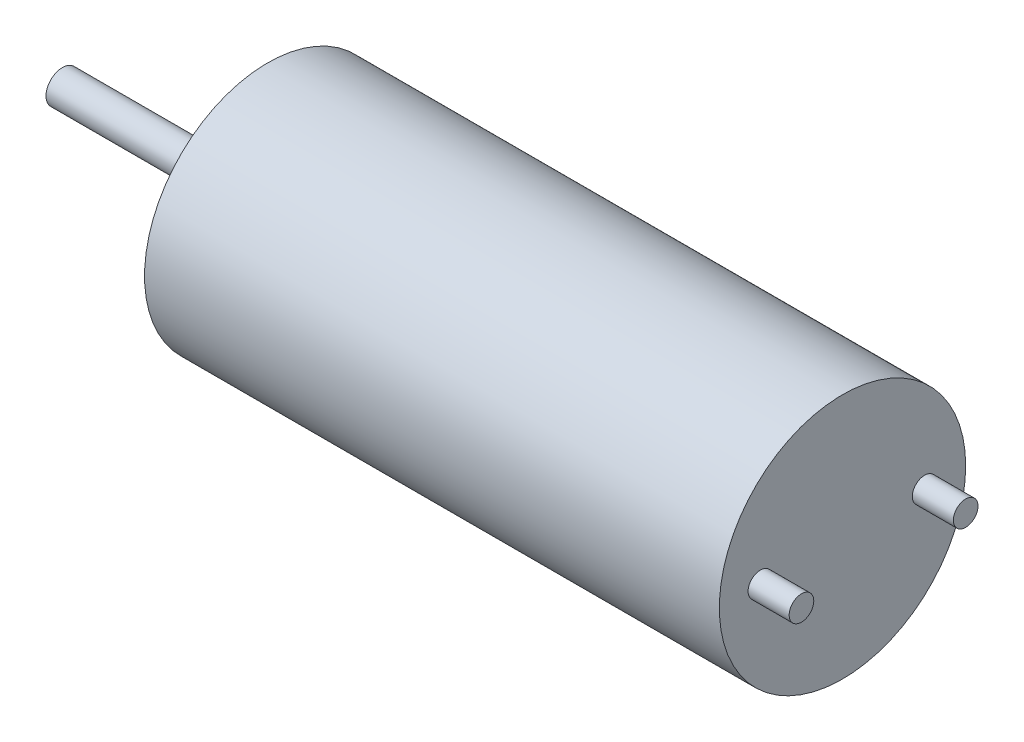
SolidWorks part; units mm, degrees
ref_plane "Front Plane" through (0, 0, 0) normal (0, 0, 1) x (1, 0, 0)
ref_plane "Top Plane" through (0, 0, 0) normal (0, 1, 0) x (1, 0, 0)
ref_plane "Right Plane" through (0, 0, 0) normal (1, 0, 0) x (0, 0, -1)
sketch "Sketch1" plane through (0, 0, 0) normal (1, 0, 0) x (0, 0, -1)
  circle A0 centre (0, 0) radius 3
  dimension "D1" = 6
extrude "Boss-Extrude1" add sketch "Sketch1" along normal blind 14
sketch "Sketch2" plane through (0, 0, 0) normal (-1, 0, 0) x (0, 0, 1)
  circle A0 centre (0, 0) radius 1.2
  dimension "D1" = 2.4
extrude "Boss-Extrude2" add sketch "Sketch2" along normal blind 0.8
sketch "Sketch3" plane through (-0.8, 0, 0) normal (-1, 0, 0) x (0, 0, 1)
  circle A0 centre (0, 0) radius 0.4
  dimension "D1" = 0.8
extrude "Boss-Extrude3" add sketch "Sketch3" along normal blind 4.2
sketch "Sketch4" plane through (14, 0, 0) normal (1, 0, 0) x (0, 0, -1)
  line L0 (-2, 0) -> (2, 0) construction
  circle A0 centre (-2, 0) radius 0.3
  circle A1 centre (2, 0) radius 0.3
  point P4 (0, 0)
  dimension "D2" = 0.6
  dimension "D1" = 4
extrude "Boss-Extrude4" add sketch "Sketch4" along normal blind 1
